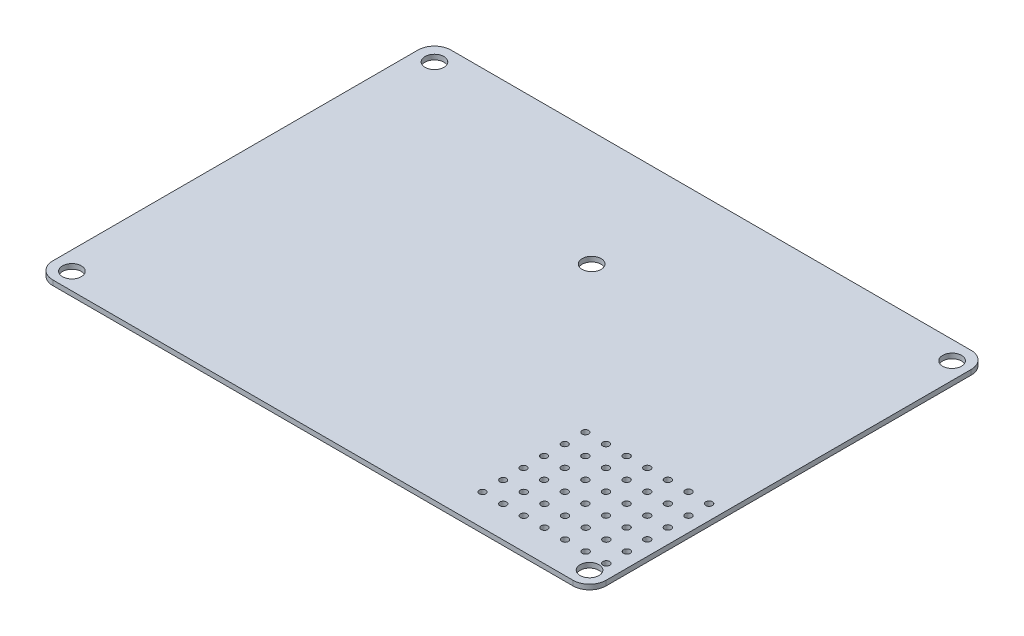
SolidWorks part; units mm, degrees
ref_plane "Plan de face" through (0, 0, 0) normal (0, 0, 1) x (1, 0, 0)
ref_plane "Plan de dessus" through (0, 0, 0) normal (0, 1, 0) x (1, 0, 0)
ref_plane "Plan de droite" through (0, 0, 0) normal (1, 0, 0) x (0, 0, -1)
sketch "Carte" plane through (0, 0, 0) normal (0, 1, 0) x (1, 0, 0)
  line L1 (4, 0) -> (130.112, 0)
  line L2 (0, -4) -> (0, -92.52)
  line L3 (4, -96.52) -> (130.112, -96.52)
  line L4 (134.112, -4) -> (134.112, -92.52)
  arc A0 (4, 0) -> (0, -4) centre (4, -4) ccw
  arc A1 (134.112, -4) -> (130.112, 0) centre (130.112, -4) ccw
  arc A2 (130.112, -96.52) -> (134.112, -92.52) centre (130.112, -92.52) ccw
  arc A3 (0, -92.52) -> (4, -96.52) centre (4, -92.52) ccw
  point P7 (0, 0)
  dimension "D1" = 4
  dimension "D2" = 134.112
  dimension "D3" = 96.52
extrude "Extrusion1" add sketch "Carte" along normal blind 1.2
sketch "Trous fixation" plane through (0, 1.2, 0) normal (0, 1, 0) x (1, 0, 0)
  line L0 (11.1034, 0) -> (-15.6749, 0) construction
  line L1 (130.112, 0) -> (4, 0) construction
  line L2 (-15.6749, 0) -> (142.74, 0) construction
  line L3 (0, -12.5153) -> (0, 5.2429) construction
  line L4 (0, -4) -> (0, -92.52) construction
  line L5 (0, 5.2429) -> (0, -109.481) construction
  line L6 (129.976, -4.5) -> (138.7469, -4.5) construction
  line L7 (138.7469, -4.5) -> (-16.535, -4.5) construction
  line L8 (129.976, -4.5) -> (129.976, -112.877) construction
  line L9 (129.976, -92.384) -> (4.5, -92.384) construction
  line L10 (4.5, -92.384) -> (4.5, -4.5) construction
  circle A0 centre (4.5, -4.5) radius 2.286
  circle A1 centre (129.976, -4.5) radius 2.286
  circle A2 centre (129.976, -92.384) radius 2.286
  circle A3 centre (4.5, -92.384) radius 2.286
  circle A4 centre (65.968, -27.868) radius 2.286
  dimension "D3" = 4.572
  dimension "D5" = 4.572
  dimension "D7" = 4.572
  dimension "D8" = 4.572
  dimension "D9" = 4.572
  dimension "D1" = 4.5
  dimension "D2" = 4.5
  dimension "D4" = 125.476
  dimension "D6" = 87.884
  dimension "D10" = 61.468
  dimension "D11" = 23.368
extrude "Enlèv. mat.-Extru.2" cut sketch "Trous fixation" against normal up to next
sketch "TexteElectrobot" plane through (0, 1.2, 0) normal (0, 1, 0) x (1, 0, 0)
  text T0 "ELECTROBOT V1.0" font "Arial Narrow" height in points 13
sketch "Esquisse3" plane through (0, 1.2, 0) normal (0, 1, 0) x (1, 0, 0)
sketch "Esquisse4" plane through (0, 1.2, 0) normal (0, 1, 0) x (1, 0, 0)
  line L0 (100.5225, -63.9443) -> (132.1697, -63.9443) construction
  line L1 (100.5225, -68.9443) -> (130.5225, -68.9443) construction
  line L2 (100.5225, -78.9443) -> (130.5225, -78.9443) construction
  line L3 (100.5225, -73.9443) -> (132.1697, -73.9443) construction
  line L4 (100.6041, -83.9443) -> (116.7896, -83.9443) construction
  line L5 (100.6041, -88.9443) -> (130.6041, -88.9443) construction
  circle A0 centre (100.5225, -63.9443) radius 0.786
  circle A1 centre (105.5225, -63.9443) radius 0.8034
  circle A2 centre (110.5225, -63.9443) radius 0.8071
  circle A3 centre (115.5225, -63.9443) radius 0.8034
  circle A4 centre (120.5225, -63.9443) radius 0.8034
  circle A5 centre (125.5225, -63.9443) radius 0.8034
  circle A6 centre (130.5225, -63.9443) radius 0.8134
  circle A7 centre (125.5225, -68.9443) radius 0.8034
  circle A8 centre (105.5225, -68.9443) radius 0.8034
  circle A9 centre (115.5225, -68.9443) radius 0.8034
  circle A10 centre (100.5225, -68.9443) radius 0.786
  circle A11 centre (120.5225, -68.9443) radius 0.8034
  circle A12 centre (110.5225, -68.9443) radius 0.8071
  circle A13 centre (130.5225, -68.9443) radius 0.8134
  circle A14 centre (105.5225, -78.9443) radius 0.8034
  circle A15 centre (115.5225, -73.9443) radius 0.8034
  circle A16 centre (120.5225, -78.9443) radius 0.8034
  circle A17 centre (110.5225, -73.9443) radius 0.8071
  circle A18 centre (100.5225, -78.9443) radius 0.786
  circle A19 centre (130.5225, -73.9443) radius 0.8134
  circle A20 centre (130.5225, -78.9443) radius 0.8134
  circle A21 centre (115.5225, -78.9443) radius 0.8034
  circle A22 centre (105.5225, -73.9443) radius 0.8034
  circle A23 centre (125.5225, -73.9443) radius 0.8034
  circle A24 centre (110.5225, -78.9443) radius 0.8071
  circle A25 centre (120.5225, -73.9443) radius 0.8034
  circle A26 centre (125.5225, -78.9443) radius 0.8034
  circle A27 centre (100.5225, -73.9443) radius 0.786
  circle A28 centre (100.6041, -83.9443) radius 0.786
  circle A29 centre (105.6041, -83.9443) radius 0.8034
  circle A30 centre (110.6041, -83.9443) radius 0.8071
  circle A31 centre (115.6041, -83.9443) radius 0.8034
  circle A32 centre (120.6041, -83.9443) radius 0.8034
  circle A33 centre (125.6041, -83.9443) radius 0.8034
  circle A34 centre (130.6041, -83.9443) radius 0.8134
  circle A35 centre (125.6041, -88.9443) radius 0.8034
  circle A36 centre (105.6041, -88.9443) radius 0.8034
  circle A37 centre (115.6041, -88.9443) radius 0.8034
  circle A38 centre (100.6041, -88.9443) radius 0.786
  circle A39 centre (120.6041, -88.9443) radius 0.8034
  circle A40 centre (110.6041, -88.9443) radius 0.8071
  circle A41 centre (130.6041, -88.9443) radius 0.8134
  dimension "D6" = 5
  dimension "D8" = 5
  dimension "D1" = 5
  dimension "D2" = 5
  dimension "D3" = 5
  dimension "D4" = 5
  dimension "D5" = 5
  dimension "D7" = 5
  dimension "D9" = 5
  dimension "D10" = 5
  dimension "D11" = 5
extrude "Enlèv. mat.-Extru.3" cut sketch "Esquisse4" against normal up to next (1.2 mm away)
sketch "TextePrototypage" plane through (0, 1.2, 0) normal (0, 1, 0) x (1, 0, 0)
  text T0 "Prototypage" font "Century Gothic" height 2.5
